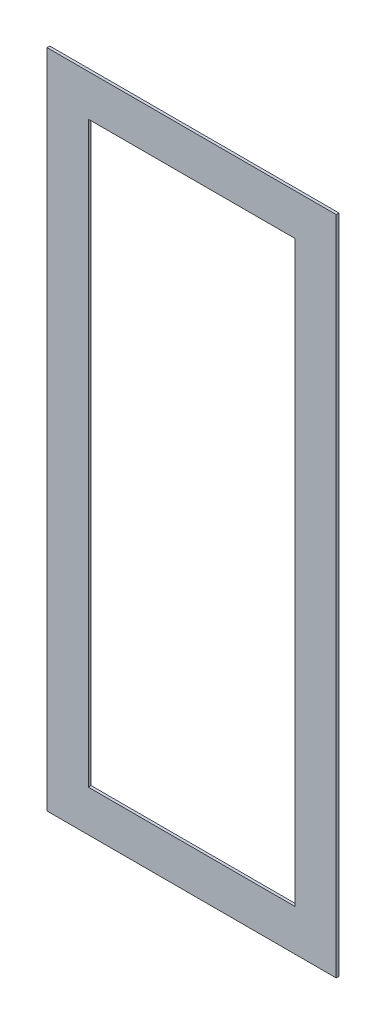
SolidWorks part; units mm, degrees
ref_plane "Front Plane" through (0, 0, 0) normal (0, 0, 1) x (1, 0, 0)
ref_plane "Top Plane" through (0, 0, 0) normal (0, 1, 0) x (1, 0, 0)
ref_plane "Right Plane" through (0, 0, 0) normal (1, 0, 0) x (0, 0, -1)
sketch "Sketch1" plane through (0, 0, 0) normal (0, 0, 1) x (1, 0, 0)
  line L0 (10.5, 24) -> (-10.5, 24)
  line L1 (7.5, 21) -> (-7.5, 21)
  line L2 (7.5, 21) -> (7.5, -21)
  line L3 (7.5, -21) -> (-7.5, -21)
  line L4 (-7.5, 21) -> (-7.5, -21)
  line L5 (7.5, 21) -> (-7.5, -21) construction
  line L6 (7.5, -21) -> (-7.5, 21) construction
  line L7 (-10.5, 24) -> (-10.5, -24)
  line L8 (10.5, -24) -> (-10.5, -24)
  line L9 (10.5, 24) -> (10.5, -24)
  point P0 (0, 0)
  dimension "D1" = 15
  dimension "D2" = 42
  dimension "D3" = 3
extrude "Boss-Extrude1" add sketch "Sketch1" along normal blind 0.2
